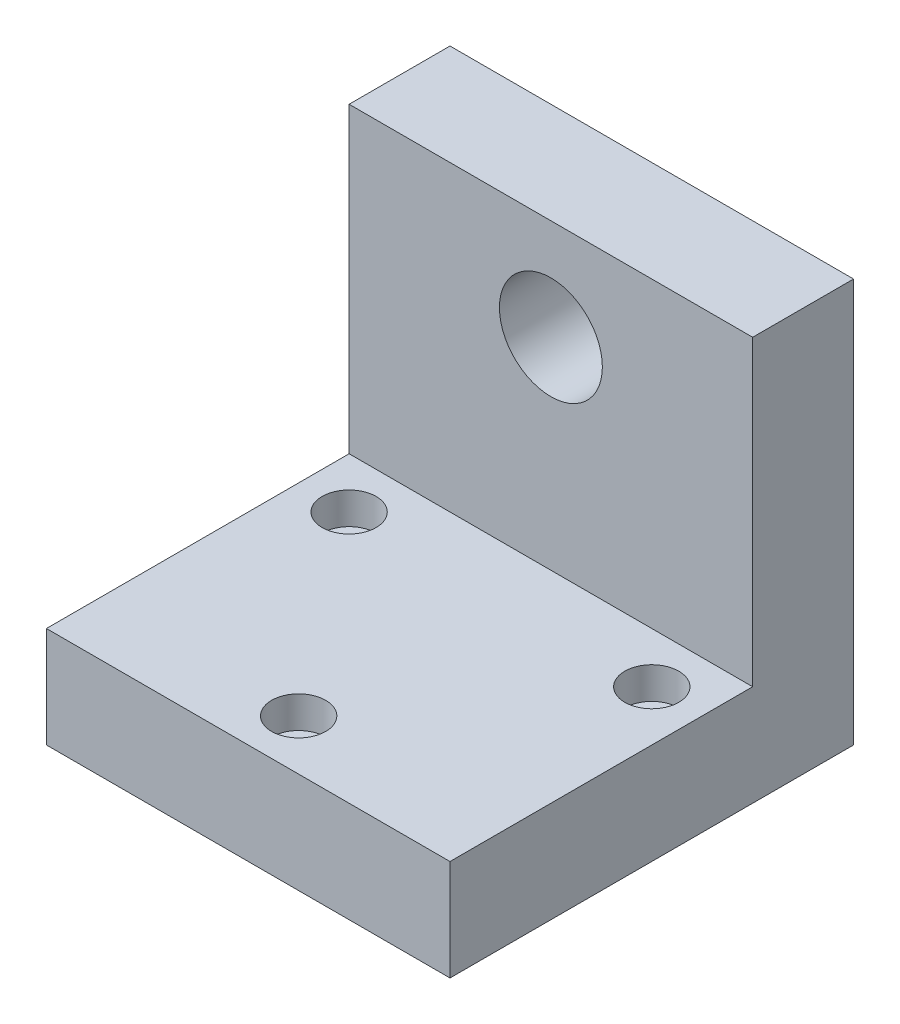
SolidWorks part; units mm, degrees
ref_plane "Front Plane" through (0, 0, 0) normal (0, 0, 1) x (1, 0, 0)
ref_plane "Top Plane" through (0, 0, 0) normal (0, 1, 0) x (1, 0, 0)
ref_plane "Right Plane" through (0, 0, 0) normal (1, 0, 0) x (0, 0, -1)
sketch "Sketch1" plane through (0, 0, 0) normal (0, 0, 1) x (1, 0, 0)
  line L1 (0, 0) -> (25.4, 0)
  line L2 (0, 0) -> (0, 25.4)
  line L3 (0, 25.4) -> (25.4, 25.4)
  line L4 (25.4, 0) -> (25.4, 25.4)
  dimension "D1" = 25.4
  dimension "D2" = 25.4
extrude "Boss-Extrude1" add sketch "Sketch1" along normal mid plane 6.35 from offset 0
sketch "Sketch2" plane through (0, 0, 3.175) normal (0, 0, 1) x (1, 0, 0)
  line L0 (0, 25.4) -> (0, 0) construction
  line L1 (0, 6.35) -> (25.4, 6.35)
  line L2 (0, 6.35) -> (0, 0)
  line L3 (0, 0) -> (25.4, 0)
  line L4 (25.4, 6.35) -> (25.4, 0)
  dimension "D1" = 6.35
extrude "Boss-Extrude2" add sketch "Sketch2" along normal blind 19.05
sketch "Sketch4" plane through (0, 6.35, 0) normal (0, 1, 0) x (1, 0, 0)
  line L0 (0, -22.225) -> (0, -3.175) construction
  line L1 (25.4, -3.175) -> (0, -3.175) construction
  line L2 (25.4, -22.225) -> (25.4, -3.175) construction
  line L3 (25.4, -22.225) -> (0, -22.225) construction
  circle A0 centre (3.175, -6.35) radius 1.127
  circle A1 centre (22.225, -6.35) radius 1.127
  circle A2 centre (12.7, -19.05) radius 1.127
  point P16 (12.7, -22.225)
  dimension "D1" = 2.254
  dimension "D2" = 3.175
  dimension "D3" = 3.175
  dimension "D4" = 3.175
  dimension "D5" = 3.175
extrude "Cut-Extrude2" cut sketch "Sketch4" against normal through all
sketch "Sketch9" plane through (0, 6.35, 0) normal (0, 1, 0) x (1, 0, 0)
  circle A0 centre (3.175, -6.35) radius 1.7
  circle A1 centre (22.225, -6.35) radius 1.7
  circle A2 centre (12.7, -19.05) radius 1.7
  dimension "D1" = 3.4
extrude "Cut-Extrude4" cut sketch "Sketch9" against normal blind 2
sketch "Sketch3" plane through (0, 0, 3.175) normal (0, 0, 1) x (1, 0, 0)
  line L6 (25.4, 25.4) -> (0, 25.4) construction
  circle A0 centre (12.7, 19.05) radius 3.2385
  point P8 (12.7, 25.4)
  dimension "D2" = 6.477
  dimension "D1" = 19.05
extrude "Cut-Extrude1" cut sketch "Sketch3" against normal through all both and the other way through all
equation "\"tightTol\"= 0.005in"
equation "\"normTol\"= 0.01in"
equation "\"looseTol\"= 0.02in"
equation "\"D2@Sketch3\"=0.25+\"tightTol\""
equation "\"D1@Sketch4\"=2mm+\"normTol\""
equation "\"D1@Sketch9\"=3.4mm"
equation "\"D1@Cut-Extrude4\"=2mm"
